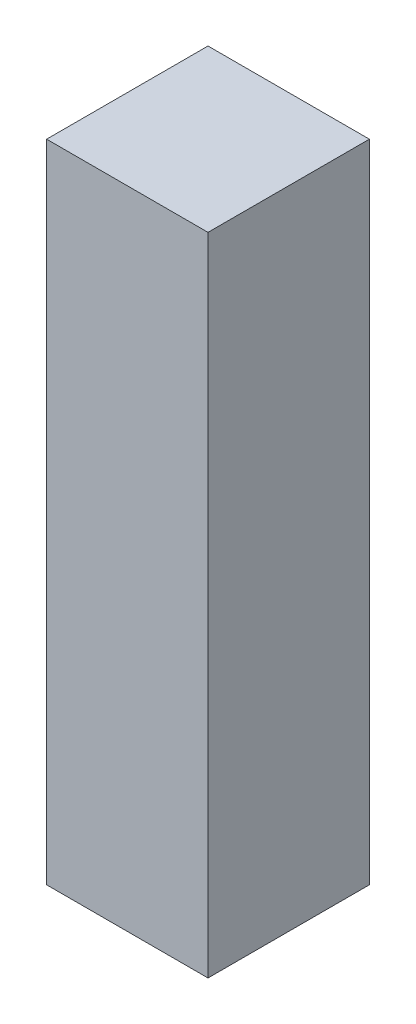
SolidWorks part; units mm, degrees
ref_plane "Front Plane" through (0, 0, 0) normal (0, 0, 1) x (1, 0, 0)
ref_plane "Top Plane" through (0, 0, 0) normal (0, 1, 0) x (1, 0, 0)
ref_plane "Right Plane" through (0, 0, 0) normal (1, 0, 0) x (0, 0, -1)
sketch "Sketch2" plane through (0, 0, 0) normal (0, 0, 1) x (1, 0, 0)
  line L1 (-1.5875, -6.3525) -> (1.5875, -6.3525)
  line L2 (-1.5875, -6.3525) -> (-1.5875, 6.3525)
  line L3 (-1.5875, 6.3525) -> (1.5875, 6.3525)
  line L4 (1.5875, -6.3525) -> (1.5875, 6.3525)
  line L5 (-1.5875, -6.3525) -> (1.5875, 6.3525) construction
  line L6 (-1.5875, 6.3525) -> (1.5875, -6.3525) construction
  point P0 (0, 0)
  dimension "D1" = 3.175
  dimension "D2" = 12.7051
extrude "Boss-Extrude1" add sketch "Sketch2" along normal blind 3.175
equation "\"side thickness\"= 1 / 8in"
equation "\"extrude thickness\"= 1 / 8in"
equation "\"length\"= 0.4522 + 0.048in"
equation "\"D1@Sketch2\"=\"side thickness\""
equation "\"D2@Sketch2\"=\"length\""
equation "\"D1@Boss-Extrude1\"=\"extrude thickness\""
